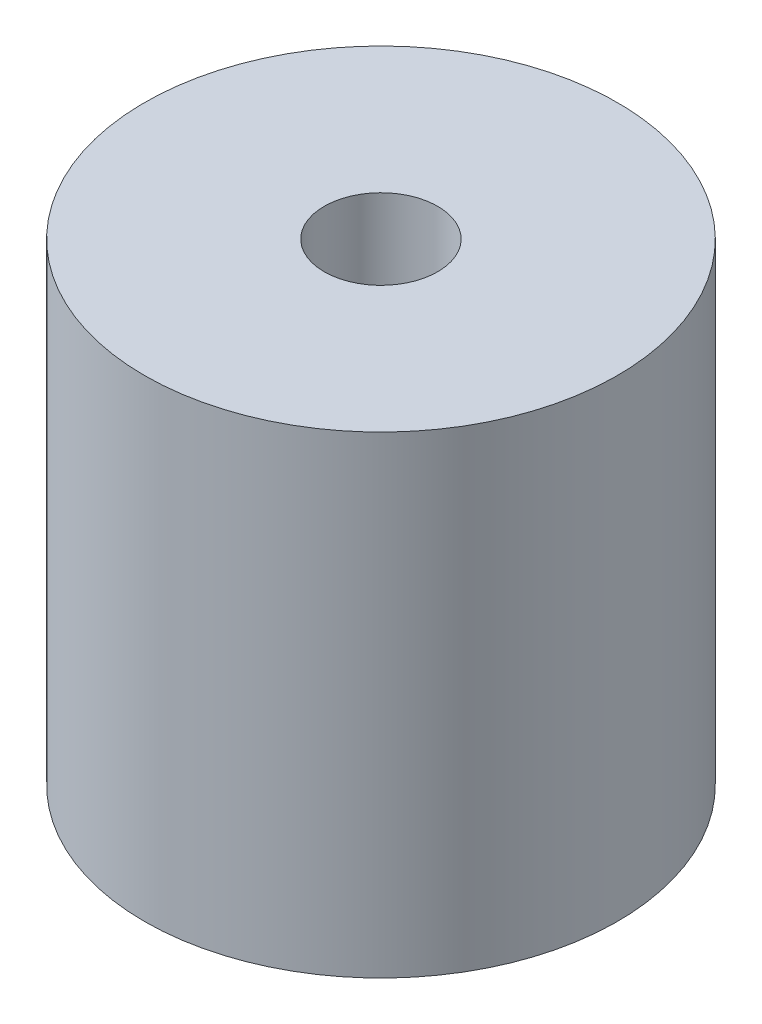
SolidWorks part; units mm, degrees
material "6061-T6 Al"
ref_plane "Front" through (0, 0, 0) normal (0, 0, 1) x (1, 0, 0)
ref_plane "Top" through (0, 0, 0) normal (0, 1, 0) x (1, 0, 0)
ref_plane "Right" through (0, 0, 0) normal (1, 0, 0) x (0, 0, -1)
sketch "Sketch1" plane through (0, 0, 0) normal (0, 1, 0) x (1, 0, 0)
  circle A0 centre (0, 0) radius 17.5
  dimension "D1" = 35
extrude "Boss-Extrude1" add sketch "Sketch1" along normal blind 35
sketch "Sketch2" plane through (0, 35, 0) normal (0, 1, 0) x (1, 0, 0)
  circle A0 centre (0, 0) radius 4.2
  dimension "D1" = 8.4
extrude "Cut-Extrude1" cut sketch "Sketch2" against normal blind 10
sketch "Sketch3" plane through (0, 25, 0) normal (0, 1, 0) x (1, 0, 0)
  circle A0 centre (0, 0) radius 1.7
  dimension "D1" = 3.4
extrude "Cut-Extrude2" cut sketch "Sketch3" against normal through all
chamfer "Chamfer1" distance 2.4892 angle 45 1 edges at (0, 25, 1.7)
